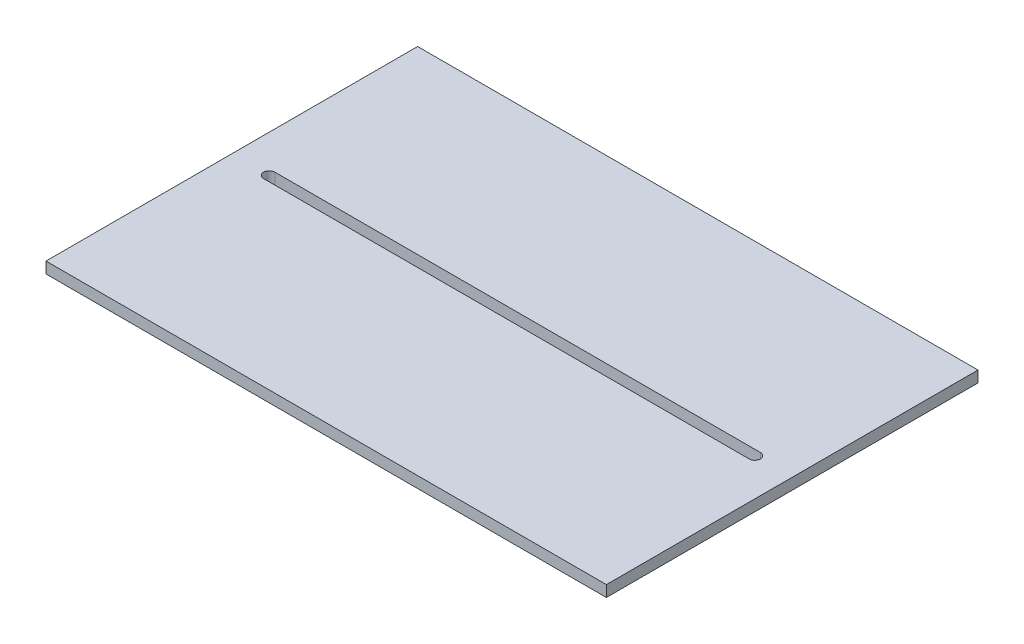
SolidWorks part; units mm, degrees
ref_plane "Front Plane" through (0, 0, 0) normal (0, 0, 1) x (1, 0, 0)
ref_plane "Top Plane" through (0, 0, 0) normal (0, 1, 0) x (1, 0, 0)
ref_plane "Right Plane" through (0, 0, 0) normal (1, 0, 0) x (0, 0, -1)
sketch "Sketch1" plane through (0, 0, 0) normal (0, 1, 0) x (1, 0, 0)
  line L0 (75, 0) -> (75, 99.4771) construction
  line L1 (0, 0) -> (150, 0)
  line L2 (0, 0) -> (0, 99.4771)
  line L3 (0, 99.4771) -> (150, 99.4771)
  line L4 (150, 0) -> (150, 99.4771)
  line L8 (140, 49.7385) -> (10, 49.7385) construction
  line L10 (140, 48.2385) -> (10, 48.2385)
  line L11 (140, 51.2385) -> (10, 51.2385)
  arc A0 (140, 48.2385) -> (140, 51.2385) centre (140, 49.7385) ccw
  arc A1 (10, 51.2385) -> (10, 48.2385) centre (10, 49.7385) ccw
  point P7 (75, 49.7385)
  point P16 (75, 49.7385)
extrude "Boss-Extrude1" add sketch "Sketch1" along normal blind 3
